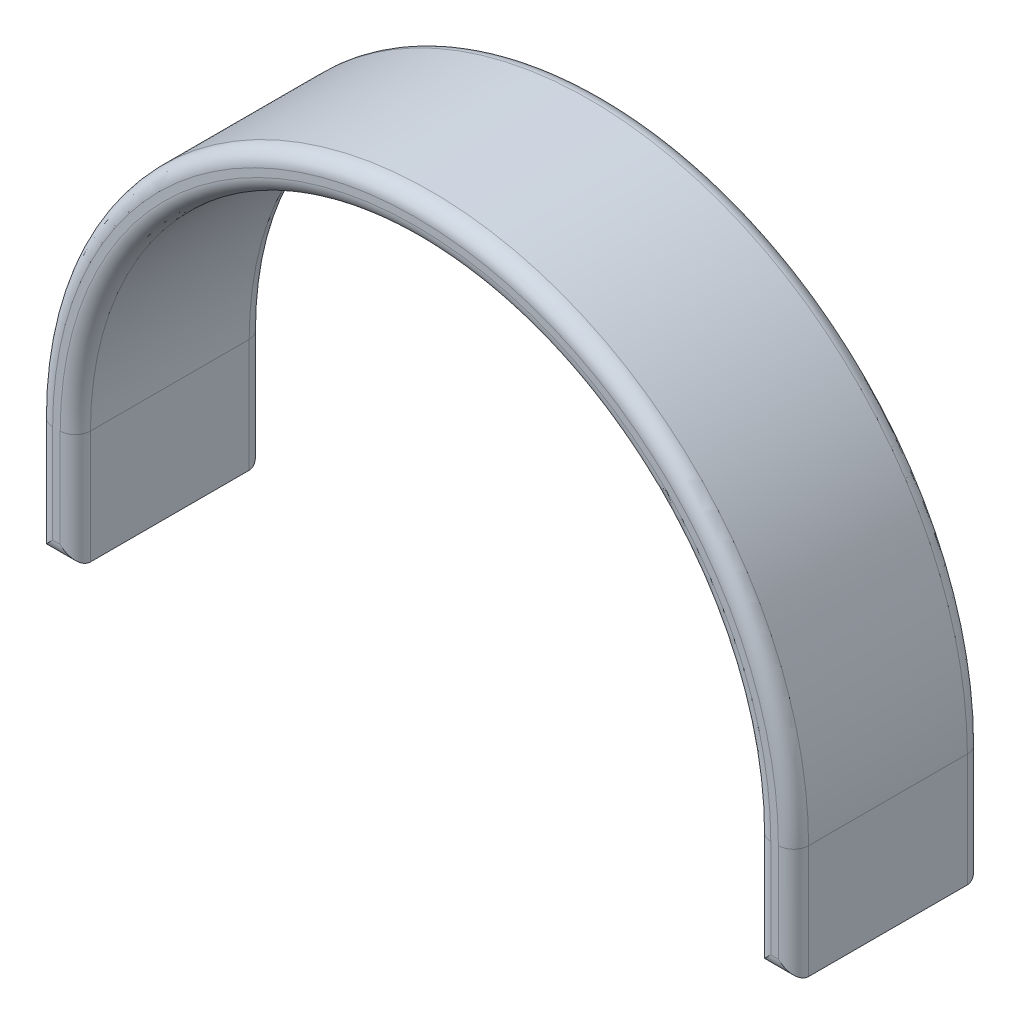
SolidWorks part; units mm, degrees
ref_plane "Front Plane" through (0, 0, 0) normal (0, 0, 1) x (1, 0, 0)
ref_plane "Top Plane" through (0, 0, 0) normal (0, 1, 0) x (1, 0, 0)
ref_plane "Right Plane" through (0, 0, 0) normal (1, 0, 0) x (0, 0, -1)
sketch "Sketch1" plane through (0, 0, 0) normal (0, 0, 1) x (1, 0, 0)
  line L0 (-50, 0) -> (-50, -15)
  line L1 (50, 0) -> (50, -15)
  line L2 (45, 0) -> (45, -15)
  line L3 (-45, 0) -> (-45, -15)
  line L4 (-50, -15) -> (-45, -15)
  line L5 (45, -15) -> (50, -15)
  line L6 (-45, -15) -> (45, -15) construction
  arc A0 (-50, 0) -> (50, 0) centre (0, 0) cw
  arc A1 (-45, 0) -> (45, 0) centre (0, 0) cw
  dimension "D2" = 50
  dimension "D3" = 15
  dimension "D1" = 5
extrude "Boss-Extrude1" add sketch "Sketch1" along normal blind 25
fillet "Fillet1" radius 2 16 edges at (-50, -7.5, 0) (-47.5, -15, 0) (-45, -7.5, 0) (0, 45, 0) (45, -7.5, 0) (47.5, -15, 0) (50, -7.5, 0) (0, 50, 0) (50, -7.5, 25) (47.5, -15, 25) (45, -7.5, 25) (0, 45, 25) (-45, -7.5, 25) (-47.5, -15, 25) (-50, -7.5, 25) (0, 50, 25)
